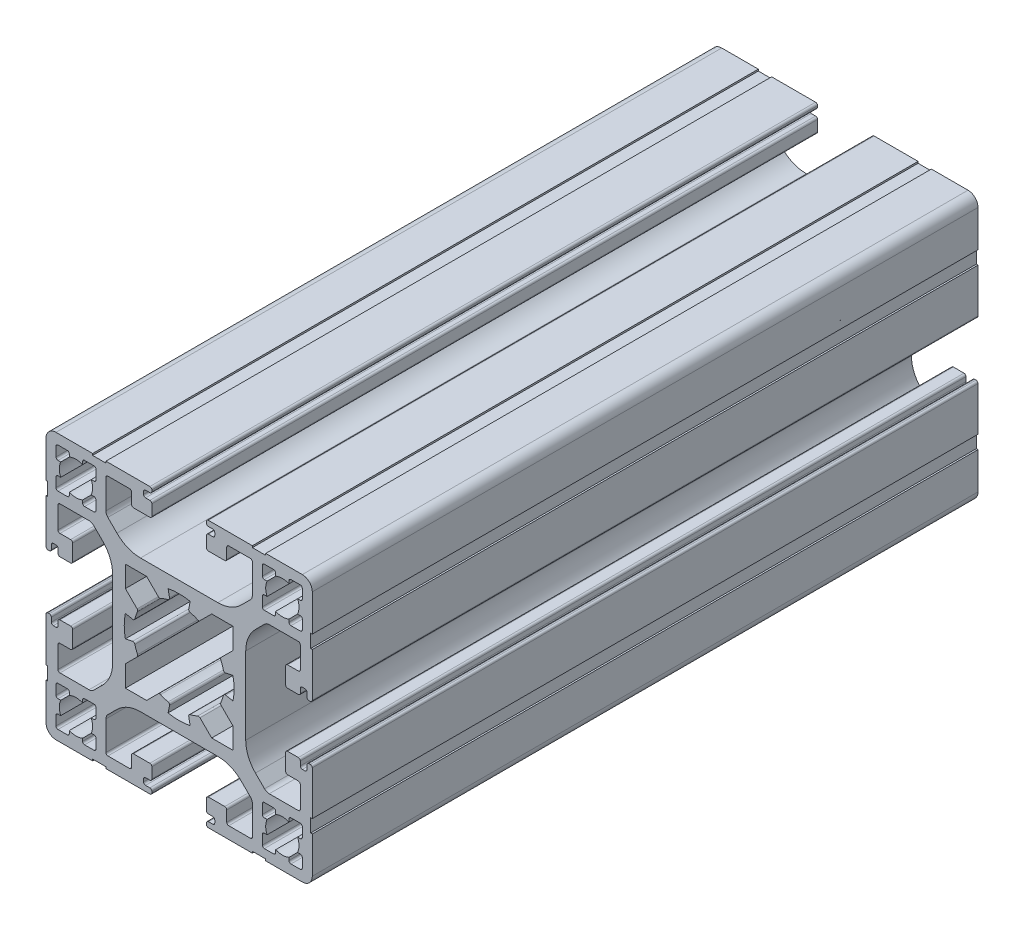
SolidWorks part; units mm, degrees
ref_plane "Plano frontal" through (0, 0, 0) normal (0, 0, 1) x (1, 0, 0)
ref_plane "Plano superior" through (0, 0, 0) normal (0, 1, 0) x (1, 0, 0)
ref_plane "Plano direito" through (0, 0, 0) normal (1, 0, 0) x (0, 0, -1)
sketch "Esboço1" plane through (0, 0, 0) normal (1, 0, 0) x (0, 0, -1)
  line L0 (-50, 0) -> (50, 0)
  point P4 (0, 0)
  dimension "D1" = 100
other "Quadrado PF40-01 - PERFIL 4040 BÁSICO(1)"
ref_plane "Plano1" through (0, 0, 50) normal (0, 0, -1) x (0, -1, 0)
sketch "Sketch1" plane through (0, 0, 50) normal (0, 0, -1) x (0, -1, 0)
  line L0 (18.2, -16.5) -> (17.7913, -16.5)
  line L1 (18.5, -18.2) -> (18.5, -16.8)
  line L2 (16.8, -18.5) -> (18.2, -18.5)
  line L3 (16.5, -17.7913) -> (16.5, -18.2)
  line L4 (14.5, -18.2) -> (14.5, -17.7913)
  line L5 (12.8, -18.5) -> (14.2, -18.5)
  line L6 (12.5, -16.8) -> (12.5, -18.2)
  line L7 (13.2087, -16.5) -> (12.8, -16.5)
  line L8 (12.8, -14.5) -> (13.2087, -14.5)
  line L9 (12.5, -12.8) -> (12.5, -14.2)
  line L10 (14.2, -12.5) -> (12.8, -12.5)
  line L11 (14.5, -13.2087) -> (14.5, -12.8)
  line L12 (16.5, -12.8) -> (16.5, -13.2087)
  line L13 (18.2, -12.5) -> (16.8, -12.5)
  line L14 (18.5, -14.2) -> (18.5, -12.8)
  line L15 (17.7913, -14.5) -> (18.2, -14.5)
  line L16 (-6.9972, 1.4391) -> (-8.0809, 1.662)
  line L17 (-8.0711, 4.8891) -> (-6.3143, 3.1324)
  line L18 (-8.0711, 8.0711) -> (-8.0711, 4.8891)
  line L19 (-4.8891, 8.0711) -> (-8.0711, 8.0711)
  line L20 (-3.1324, 6.3143) -> (-4.8891, 8.0711)
  line L21 (-1.662, 8.0809) -> (-1.4391, 6.9972)
  line L22 (1.4391, 6.9972) -> (1.662, 8.0809)
  line L23 (4.8891, 8.0711) -> (3.1324, 6.3143)
  line L24 (8.0711, 8.0711) -> (4.8891, 8.0711)
  line L25 (8.0711, 4.8891) -> (8.0711, 8.0711)
  line L26 (6.3143, 3.1324) -> (8.0711, 4.8891)
  line L27 (8.0809, 1.662) -> (6.9972, 1.4391)
  line L28 (6.9972, -1.4391) -> (8.0809, -1.662)
  line L29 (8.0711, -4.8891) -> (6.3143, -3.1324)
  line L30 (8.0711, -8.0711) -> (8.0711, -4.8891)
  line L31 (4.8891, -8.0711) -> (8.0711, -8.0711)
  line L32 (3.1324, -6.3143) -> (4.8891, -8.0711)
  line L33 (1.662, -8.0809) -> (1.4391, -6.9972)
  line L34 (-1.4391, -6.9972) -> (-1.662, -8.0809)
  line L35 (-4.8891, -8.0711) -> (-3.1324, -6.3143)
  line L36 (-8.0711, -8.0711) -> (-4.8891, -8.0711)
  line L37 (-8.0711, -4.8891) -> (-8.0711, -8.0711)
  line L38 (-6.3143, -3.1324) -> (-8.0711, -4.8891)
  line L39 (-8.0809, -1.662) -> (-6.9972, -1.4391)
  line L40 (-9.3431, 11.4645) -> (-10.7071, 12.8284)
  line L41 (-11, 13.5355) -> (-11, 17.9)
  line L42 (-10.7, 18.2) -> (-7.45, 18.2)
  line L43 (-7.15, 17.9) -> (-7.15, 16.3)
  line L44 (-6.85, 16) -> (-4.4, 16)
  line L45 (-4.1, 16.3) -> (-4.1, 17.9)
  line L46 (-4.4, 18.2) -> (-5.05, 18.2)
  line L47 (-5.35, 18.5) -> (-5.35, 18.9)
  line L48 (-5.05, 19.2) -> (-4.4, 19.2)
  line L49 (-4.1, 19.5) -> (-4.1, 19.7)
  line L50 (-4.4, 20) -> (-11, 20)
  line L51 (-11, 20) -> (-11, 19.75)
  line L52 (-11, 19.75) -> (-13, 19.75)
  line L53 (-13, 19.75) -> (-13, 20)
  line L54 (-13, 20) -> (-18.5, 20)
  line L55 (-20, 18.5) -> (-20, 13)
  line L56 (-20, 13) -> (-19.75, 13)
  line L57 (-19.75, 13) -> (-19.75, 11)
  line L58 (-19.75, 11) -> (-20, 11)
  line L59 (-20, 11) -> (-20, 4.4)
  line L60 (-19.7, 4.1) -> (-19.5, 4.1)
  line L61 (-19.2, 4.4) -> (-19.2, 5.05)
  line L62 (-18.9, 5.35) -> (-18.5, 5.35)
  line L63 (-18.2, 5.05) -> (-18.2, 4.4)
  line L64 (-17.9, 4.1) -> (-16.3, 4.1)
  line L65 (-16, 4.4) -> (-16, 6.85)
  line L66 (-16.3, 7.15) -> (-17.9, 7.15)
  line L67 (-18.2, 7.45) -> (-18.2, 10.7)
  line L68 (-17.9, 11) -> (-13.5355, 11)
  line L69 (-12.8284, 10.7071) -> (-11.4645, 9.3431)
  line L70 (-10, 5.8076) -> (-10, -5.8076)
  line L71 (-11.4645, -9.3431) -> (-12.8284, -10.7071)
  line L72 (-13.5355, -11) -> (-17.9, -11)
  line L73 (-18.2, -10.7) -> (-18.2, -7.45)
  line L74 (-17.9, -7.15) -> (-16.3, -7.15)
  line L75 (-16, -6.85) -> (-16, -4.4)
  line L76 (-16.3, -4.1) -> (-17.9, -4.1)
  line L77 (-18.2, -4.4) -> (-18.2, -5.05)
  line L78 (-18.5, -5.35) -> (-18.9, -5.35)
  line L79 (-19.2, -5.05) -> (-19.2, -4.4)
  line L80 (-19.5, -4.1) -> (-19.7, -4.1)
  line L81 (-20, -4.4) -> (-20, -11)
  line L82 (-20, -11) -> (-19.75, -11)
  line L83 (-19.75, -11) -> (-19.75, -13)
  line L84 (-19.75, -13) -> (-20, -13)
  line L85 (-20, -13) -> (-20, -18.5)
  line L86 (-18.5, -20) -> (-13, -20)
  line L87 (-13, -20) -> (-13, -19.75)
  line L88 (-13, -19.75) -> (-11, -19.75)
  line L89 (-11, -19.75) -> (-11, -20)
  line L90 (-11, -20) -> (-4.4, -20)
  line L91 (-4.1, -19.7) -> (-4.1, -19.5)
  line L92 (-4.4, -19.2) -> (-5.05, -19.2)
  line L93 (-5.35, -18.9) -> (-5.35, -18.5)
  line L94 (-5.05, -18.2) -> (-4.4, -18.2)
  line L95 (-4.1, -17.9) -> (-4.1, -16.3)
  line L96 (-4.4, -16) -> (-6.85, -16)
  line L97 (-7.15, -16.3) -> (-7.15, -17.9)
  line L98 (-7.45, -18.2) -> (-10.7, -18.2)
  line L99 (-11, -17.9) -> (-11, -13.5355)
  line L100 (-10.7071, -12.8284) -> (-9.3431, -11.4645)
  line L101 (-5.8076, -10) -> (5.8076, -10)
  line L102 (9.3431, -11.4645) -> (10.7071, -12.8284)
  line L103 (11, -13.5355) -> (11, -17.9)
  line L104 (10.7, -18.2) -> (7.45, -18.2)
  line L105 (7.15, -17.9) -> (7.15, -16.3)
  line L106 (6.85, -16) -> (4.4, -16)
  line L107 (4.1, -16.3) -> (4.1, -17.9)
  line L108 (4.4, -18.2) -> (5.05, -18.2)
  line L109 (5.35, -18.5) -> (5.35, -18.9)
  line L110 (5.05, -19.2) -> (4.4, -19.2)
  line L111 (4.1, -19.5) -> (4.1, -19.7)
  line L112 (4.4, -20) -> (11, -20)
  line L113 (11, -20) -> (11, -19.75)
  line L114 (11, -19.75) -> (13, -19.75)
  line L115 (13, -19.75) -> (13, -20)
  line L116 (13, -20) -> (18.5, -20)
  line L117 (20, -18.5) -> (20, -13)
  line L118 (20, -13) -> (19.75, -13)
  line L119 (19.75, -13) -> (19.75, -11)
  line L120 (19.75, -11) -> (20, -11)
  line L121 (20, -11) -> (20, -4.4)
  line L122 (19.7, -4.1) -> (19.5, -4.1)
  line L123 (19.2, -4.4) -> (19.2, -5.05)
  line L124 (18.9, -5.35) -> (18.5, -5.35)
  line L125 (18.2, -5.05) -> (18.2, -4.4)
  line L126 (17.9, -4.1) -> (16.3, -4.1)
  line L127 (16, -4.4) -> (16, -6.85)
  line L128 (16.3, -7.15) -> (17.9, -7.15)
  line L129 (18.2, -7.45) -> (18.2, -10.7)
  line L130 (17.9, -11) -> (13.5355, -11)
  line L131 (12.8284, -10.7071) -> (11.4645, -9.3431)
  line L132 (10, -5.8076) -> (10, 5.8076)
  line L133 (11.4645, 9.3431) -> (12.8284, 10.7071)
  line L134 (13.5355, 11) -> (17.9, 11)
  line L135 (18.2, 10.7) -> (18.2, 7.45)
  line L136 (17.9, 7.15) -> (16.3, 7.15)
  line L137 (16, 6.85) -> (16, 4.4)
  line L138 (16.3, 4.1) -> (17.9, 4.1)
  line L139 (18.2, 4.4) -> (18.2, 5.05)
  line L140 (18.5, 5.35) -> (18.9, 5.35)
  line L141 (19.2, 5.05) -> (19.2, 4.4)
  line L142 (19.5, 4.1) -> (19.7, 4.1)
  line L143 (20, 4.4) -> (20, 11)
  line L144 (20, 11) -> (19.75, 11)
  line L145 (19.75, 11) -> (19.75, 13)
  line L146 (19.75, 13) -> (20, 13)
  line L147 (20, 13) -> (20, 18.5)
  line L148 (18.5, 20) -> (13, 20)
  line L149 (13, 20) -> (13, 19.75)
  line L150 (13, 19.75) -> (11, 19.75)
  line L151 (11, 19.75) -> (11, 20)
  line L152 (11, 20) -> (4.4, 20)
  line L153 (4.1, 19.7) -> (4.1, 19.5)
  line L154 (4.4, 19.2) -> (5.05, 19.2)
  line L155 (5.35, 18.9) -> (5.35, 18.5)
  line L156 (5.05, 18.2) -> (4.4, 18.2)
  line L157 (4.1, 17.9) -> (4.1, 16.3)
  line L158 (4.4, 16) -> (6.85, 16)
  line L159 (7.15, 16.3) -> (7.15, 17.9)
  line L160 (7.45, 18.2) -> (10.7, 18.2)
  line L161 (11, 17.9) -> (11, 13.5355)
  line L162 (10.7071, 12.8284) -> (9.3431, 11.4645)
  line L163 (5.8076, 10) -> (-5.8076, 10)
  line L164 (-16.5, 17.7913) -> (-16.5, 18.2)
  line L165 (-14.5, 18.2) -> (-14.5, 17.7913)
  line L166 (-12.8, 18.5) -> (-14.2, 18.5)
  line L167 (-12.5, 16.8) -> (-12.5, 18.2)
  line L168 (-13.2087, 16.5) -> (-12.8, 16.5)
  line L169 (-12.8, 14.5) -> (-13.2087, 14.5)
  line L170 (-12.5, 12.8) -> (-12.5, 14.2)
  line L171 (-14.2, 12.5) -> (-12.8, 12.5)
  line L172 (-14.5, 13.2087) -> (-14.5, 12.8)
  line L173 (-16.5, 12.8) -> (-16.5, 13.2087)
  line L174 (-18.2, 12.5) -> (-16.8, 12.5)
  line L175 (-18.5, 14.2) -> (-18.5, 12.8)
  line L176 (-17.7913, 14.5) -> (-18.2, 14.5)
  line L177 (-18.2, 16.5) -> (-17.7913, 16.5)
  line L178 (-18.5, 18.2) -> (-18.5, 16.8)
  line L179 (-16.8, 18.5) -> (-18.2, 18.5)
  line L180 (14.5, 17.7913) -> (14.5, 18.2)
  line L181 (16.5, 18.2) -> (16.5, 17.7913)
  line L182 (18.2, 18.5) -> (16.8, 18.5)
  line L183 (18.5, 16.8) -> (18.5, 18.2)
  line L184 (17.7913, 16.5) -> (18.2, 16.5)
  line L185 (18.2, 14.5) -> (17.7913, 14.5)
  line L186 (18.5, 12.8) -> (18.5, 14.2)
  line L187 (16.8, 12.5) -> (18.2, 12.5)
  line L188 (16.5, 13.2087) -> (16.5, 12.8)
  line L189 (14.5, 12.8) -> (14.5, 13.2087)
  line L190 (12.8, 12.5) -> (14.2, 12.5)
  line L191 (12.5, 14.2) -> (12.5, 12.8)
  line L192 (13.2087, 14.5) -> (12.8, 14.5)
  line L193 (12.8, 16.5) -> (13.2087, 16.5)
  line L194 (12.5, 18.2) -> (12.5, 16.8)
  line L195 (14.2, 18.5) -> (12.8, 18.5)
  line L196 (-14.5, -17.7913) -> (-14.5, -18.2)
  line L197 (-16.5, -18.2) -> (-16.5, -17.7913)
  line L198 (-18.2, -18.5) -> (-16.8, -18.5)
  line L199 (-18.5, -16.8) -> (-18.5, -18.2)
  line L200 (-17.7913, -16.5) -> (-18.2, -16.5)
  line L201 (-18.2, -14.5) -> (-17.7913, -14.5)
  line L202 (-18.5, -12.8) -> (-18.5, -14.2)
  line L203 (-16.8, -12.5) -> (-18.2, -12.5)
  line L204 (-16.5, -13.2087) -> (-16.5, -12.8)
  line L205 (-14.5, -12.8) -> (-14.5, -13.2087)
  line L206 (-12.8, -12.5) -> (-14.2, -12.5)
  line L207 (-12.5, -14.2) -> (-12.5, -12.8)
  line L208 (-13.2087, -14.5) -> (-12.8, -14.5)
  line L209 (-12.8, -16.5) -> (-13.2087, -16.5)
  line L210 (-12.5, -18.2) -> (-12.5, -16.8)
  line L211 (-14.2, -18.5) -> (-12.8, -18.5)
  arc A0 (18.5, -16.8) -> (18.2, -16.5) centre (18.2, -16.8) ccw
  arc A1 (18.2, -18.5) -> (18.5, -18.2) centre (18.2, -18.2) ccw
  arc A2 (16.5, -18.2) -> (16.8, -18.5) centre (16.8, -18.2) ccw
  arc A3 (14.5, -17.7913) -> (16.5, -17.7913) centre (15.5, -15.5) ccw
  arc A4 (14.2, -18.5) -> (14.5, -18.2) centre (14.2, -18.2) ccw
  arc A5 (12.5, -18.2) -> (12.8, -18.5) centre (12.8, -18.2) ccw
  arc A6 (12.8, -16.5) -> (12.5, -16.8) centre (12.8, -16.8) ccw
  arc A7 (13.2087, -14.5) -> (13.2087, -16.5) centre (15.5, -15.5) ccw
  arc A8 (12.5, -14.2) -> (12.8, -14.5) centre (12.8, -14.2) ccw
  arc A9 (12.8, -12.5) -> (12.5, -12.8) centre (12.8, -12.8) ccw
  arc A10 (14.5, -12.8) -> (14.2, -12.5) centre (14.2, -12.8) ccw
  arc A11 (16.5, -13.2087) -> (14.5, -13.2087) centre (15.5, -15.5) ccw
  arc A12 (16.8, -12.5) -> (16.5, -12.8) centre (16.8, -12.8) ccw
  arc A13 (18.5, -12.8) -> (18.2, -12.5) centre (18.2, -12.8) ccw
  arc A14 (18.2, -14.5) -> (18.5, -14.2) centre (18.2, -14.2) ccw
  arc A15 (17.7913, -16.5) -> (17.7913, -14.5) centre (15.5, -15.5) ccw
  arc A16 (-6.9972, 1.4391) -> (-6.6458, 1.6602) centre (-6.9368, 1.7329) ccw
  arc A17 (-6.2526, 2.7977) -> (-6.6458, 1.6602) centre (0, 0) ccw
  arc A18 (-6.2526, 2.7977) -> (-6.3143, 3.1324) centre (-6.5265, 2.9202) ccw
  arc A19 (-3.1324, 6.3143) -> (-2.7977, 6.2526) centre (-2.9202, 6.5265) ccw
  arc A20 (-1.6602, 6.6458) -> (-2.7977, 6.2526) centre (0, 0) ccw
  arc A21 (-1.6602, 6.6458) -> (-1.4391, 6.9972) centre (-1.7329, 6.9368) ccw
  arc A22 (1.662, 8.0809) -> (-1.662, 8.0809) centre (0, 0) ccw
  arc A23 (1.4391, 6.9972) -> (1.6602, 6.6458) centre (1.7329, 6.9368) ccw
  arc A24 (2.7977, 6.2526) -> (1.6602, 6.6458) centre (0, 0) ccw
  arc A25 (2.7977, 6.2526) -> (3.1324, 6.3143) centre (2.9202, 6.5265) ccw
  arc A26 (6.3143, 3.1324) -> (6.2526, 2.7977) centre (6.5265, 2.9202) ccw
  arc A27 (6.6458, 1.6602) -> (6.2526, 2.7977) centre (0, 0) ccw
  arc A28 (6.6458, 1.6602) -> (6.9972, 1.4391) centre (6.9368, 1.7329) ccw
  arc A29 (8.0809, -1.662) -> (8.0809, 1.662) centre (0, 0) ccw
  arc A30 (6.9972, -1.4391) -> (6.6458, -1.6602) centre (6.9368, -1.7329) ccw
  arc A31 (6.2526, -2.7977) -> (6.6458, -1.6602) centre (0, 0) ccw
  arc A32 (6.2526, -2.7977) -> (6.3143, -3.1324) centre (6.5265, -2.9202) ccw
  arc A33 (3.1324, -6.3143) -> (2.7977, -6.2526) centre (2.9202, -6.5265) ccw
  arc A34 (1.6602, -6.6458) -> (2.7977, -6.2526) centre (0, 0) ccw
  arc A35 (1.6602, -6.6458) -> (1.4391, -6.9972) centre (1.7329, -6.9368) ccw
  arc A36 (-1.662, -8.0809) -> (1.662, -8.0809) centre (0, 0) ccw
  arc A37 (-1.4391, -6.9972) -> (-1.6602, -6.6458) centre (-1.7329, -6.9368) ccw
  arc A38 (-2.7977, -6.2526) -> (-1.6602, -6.6458) centre (0, 0) ccw
  arc A39 (-2.7977, -6.2526) -> (-3.1324, -6.3143) centre (-2.9202, -6.5265) ccw
  arc A40 (-6.3143, -3.1324) -> (-6.2526, -2.7977) centre (-6.5265, -2.9202) ccw
  arc A41 (-6.6458, -1.6602) -> (-6.2526, -2.7977) centre (0, 0) ccw
  arc A42 (-6.6458, -1.6602) -> (-6.9972, -1.4391) centre (-6.9368, -1.7329) ccw
  arc A43 (-8.0809, 1.662) -> (-8.0809, -1.662) centre (0, 0) ccw
  arc A44 (-9.3431, 11.4645) -> (-5.8076, 10) centre (-5.8076, 15) ccw
  arc A45 (-11, 13.5355) -> (-10.7071, 12.8284) centre (-10, 13.5355) ccw
  arc A46 (-10.7, 18.2) -> (-11, 17.9) centre (-10.7, 17.9) ccw
  arc A47 (-7.15, 17.9) -> (-7.45, 18.2) centre (-7.45, 17.9) ccw
  arc A48 (-7.15, 16.3) -> (-6.85, 16) centre (-6.85, 16.3) ccw
  arc A49 (-4.4, 16) -> (-4.1, 16.3) centre (-4.4, 16.3) ccw
  arc A50 (-4.1, 17.9) -> (-4.4, 18.2) centre (-4.4, 17.9) ccw
  arc A51 (-5.35, 18.5) -> (-5.05, 18.2) centre (-5.05, 18.5) ccw
  arc A52 (-5.05, 19.2) -> (-5.35, 18.9) centre (-5.05, 18.9) ccw
  arc A53 (-4.4, 19.2) -> (-4.1, 19.5) centre (-4.4, 19.5) ccw
  arc A54 (-4.1, 19.7) -> (-4.4, 20) centre (-4.4, 19.7) ccw
  arc A55 (-18.5, 20) -> (-20, 18.5) centre (-18.5, 18.5) ccw
  arc A56 (-20, 4.4) -> (-19.7, 4.1) centre (-19.7, 4.4) ccw
  arc A57 (-19.5, 4.1) -> (-19.2, 4.4) centre (-19.5, 4.4) ccw
  arc A58 (-18.9, 5.35) -> (-19.2, 5.05) centre (-18.9, 5.05) ccw
  arc A59 (-18.2, 5.05) -> (-18.5, 5.35) centre (-18.5, 5.05) ccw
  arc A60 (-18.2, 4.4) -> (-17.9, 4.1) centre (-17.9, 4.4) ccw
  arc A61 (-16.3, 4.1) -> (-16, 4.4) centre (-16.3, 4.4) ccw
  arc A62 (-16, 6.85) -> (-16.3, 7.15) centre (-16.3, 6.85) ccw
  arc A63 (-18.2, 7.45) -> (-17.9, 7.15) centre (-17.9, 7.45) ccw
  arc A64 (-17.9, 11) -> (-18.2, 10.7) centre (-17.9, 10.7) ccw
  arc A65 (-12.8284, 10.7071) -> (-13.5355, 11) centre (-13.5355, 10) ccw
  arc A66 (-10, 5.8076) -> (-11.4645, 9.3431) centre (-15, 5.8076) ccw
  arc A67 (-11.4645, -9.3431) -> (-10, -5.8076) centre (-15, -5.8076) ccw
  arc A68 (-13.5355, -11) -> (-12.8284, -10.7071) centre (-13.5355, -10) ccw
  arc A69 (-18.2, -10.7) -> (-17.9, -11) centre (-17.9, -10.7) ccw
  arc A70 (-17.9, -7.15) -> (-18.2, -7.45) centre (-17.9, -7.45) ccw
  arc A71 (-16.3, -7.15) -> (-16, -6.85) centre (-16.3, -6.85) ccw
  arc A72 (-16, -4.4) -> (-16.3, -4.1) centre (-16.3, -4.4) ccw
  arc A73 (-17.9, -4.1) -> (-18.2, -4.4) centre (-17.9, -4.4) ccw
  arc A74 (-18.5, -5.35) -> (-18.2, -5.05) centre (-18.5, -5.05) ccw
  arc A75 (-19.2, -5.05) -> (-18.9, -5.35) centre (-18.9, -5.05) ccw
  arc A76 (-19.2, -4.4) -> (-19.5, -4.1) centre (-19.5, -4.4) ccw
  arc A77 (-19.7, -4.1) -> (-20, -4.4) centre (-19.7, -4.4) ccw
  arc A78 (-20, -18.5) -> (-18.5, -20) centre (-18.5, -18.5) ccw
  arc A79 (-4.4, -20) -> (-4.1, -19.7) centre (-4.4, -19.7) ccw
  arc A80 (-4.1, -19.5) -> (-4.4, -19.2) centre (-4.4, -19.5) ccw
  arc A81 (-5.35, -18.9) -> (-5.05, -19.2) centre (-5.05, -18.9) ccw
  arc A82 (-5.05, -18.2) -> (-5.35, -18.5) centre (-5.05, -18.5) ccw
  arc A83 (-4.4, -18.2) -> (-4.1, -17.9) centre (-4.4, -17.9) ccw
  arc A84 (-4.1, -16.3) -> (-4.4, -16) centre (-4.4, -16.3) ccw
  arc A85 (-6.85, -16) -> (-7.15, -16.3) centre (-6.85, -16.3) ccw
  arc A86 (-7.45, -18.2) -> (-7.15, -17.9) centre (-7.45, -17.9) ccw
  arc A87 (-11, -17.9) -> (-10.7, -18.2) centre (-10.7, -17.9) ccw
  arc A88 (-10.7071, -12.8284) -> (-11, -13.5355) centre (-10, -13.5355) ccw
  arc A89 (-5.8076, -10) -> (-9.3431, -11.4645) centre (-5.8076, -15) ccw
  arc A90 (9.3431, -11.4645) -> (5.8076, -10) centre (5.8076, -15) ccw
  arc A91 (11, -13.5355) -> (10.7071, -12.8284) centre (10, -13.5355) ccw
  arc A92 (10.7, -18.2) -> (11, -17.9) centre (10.7, -17.9) ccw
  arc A93 (7.15, -17.9) -> (7.45, -18.2) centre (7.45, -17.9) ccw
  arc A94 (7.15, -16.3) -> (6.85, -16) centre (6.85, -16.3) ccw
  arc A95 (4.4, -16) -> (4.1, -16.3) centre (4.4, -16.3) ccw
  arc A96 (4.1, -17.9) -> (4.4, -18.2) centre (4.4, -17.9) ccw
  arc A97 (5.35, -18.5) -> (5.05, -18.2) centre (5.05, -18.5) ccw
  arc A98 (5.05, -19.2) -> (5.35, -18.9) centre (5.05, -18.9) ccw
  arc A99 (4.4, -19.2) -> (4.1, -19.5) centre (4.4, -19.5) ccw
  arc A100 (4.1, -19.7) -> (4.4, -20) centre (4.4, -19.7) ccw
  arc A101 (18.5, -20) -> (20, -18.5) centre (18.5, -18.5) ccw
  arc A102 (20, -4.4) -> (19.7, -4.1) centre (19.7, -4.4) ccw
  arc A103 (19.5, -4.1) -> (19.2, -4.4) centre (19.5, -4.4) ccw
  arc A104 (18.9, -5.35) -> (19.2, -5.05) centre (18.9, -5.05) ccw
  arc A105 (18.2, -5.05) -> (18.5, -5.35) centre (18.5, -5.05) ccw
  arc A106 (18.2, -4.4) -> (17.9, -4.1) centre (17.9, -4.4) ccw
  arc A107 (16.3, -4.1) -> (16, -4.4) centre (16.3, -4.4) ccw
  arc A108 (16, -6.85) -> (16.3, -7.15) centre (16.3, -6.85) ccw
  arc A109 (18.2, -7.45) -> (17.9, -7.15) centre (17.9, -7.45) ccw
  arc A110 (17.9, -11) -> (18.2, -10.7) centre (17.9, -10.7) ccw
  arc A111 (12.8284, -10.7071) -> (13.5355, -11) centre (13.5355, -10) ccw
  arc A112 (10, -5.8076) -> (11.4645, -9.3431) centre (15, -5.8076) ccw
  arc A113 (11.4645, 9.3431) -> (10, 5.8076) centre (15, 5.8076) ccw
  arc A114 (13.5355, 11) -> (12.8284, 10.7071) centre (13.5355, 10) ccw
  arc A115 (18.2, 10.7) -> (17.9, 11) centre (17.9, 10.7) ccw
  arc A116 (17.9, 7.15) -> (18.2, 7.45) centre (17.9, 7.45) ccw
  arc A117 (16.3, 7.15) -> (16, 6.85) centre (16.3, 6.85) ccw
  arc A118 (16, 4.4) -> (16.3, 4.1) centre (16.3, 4.4) ccw
  arc A119 (17.9, 4.1) -> (18.2, 4.4) centre (17.9, 4.4) ccw
  arc A120 (18.5, 5.35) -> (18.2, 5.05) centre (18.5, 5.05) ccw
  arc A121 (19.2, 5.05) -> (18.9, 5.35) centre (18.9, 5.05) ccw
  arc A122 (19.2, 4.4) -> (19.5, 4.1) centre (19.5, 4.4) ccw
  arc A123 (19.7, 4.1) -> (20, 4.4) centre (19.7, 4.4) ccw
  arc A124 (20, 18.5) -> (18.5, 20) centre (18.5, 18.5) ccw
  arc A125 (4.4, 20) -> (4.1, 19.7) centre (4.4, 19.7) ccw
  arc A126 (4.1, 19.5) -> (4.4, 19.2) centre (4.4, 19.5) ccw
  arc A127 (5.35, 18.9) -> (5.05, 19.2) centre (5.05, 18.9) ccw
  arc A128 (5.05, 18.2) -> (5.35, 18.5) centre (5.05, 18.5) ccw
  arc A129 (4.4, 18.2) -> (4.1, 17.9) centre (4.4, 17.9) ccw
  arc A130 (4.1, 16.3) -> (4.4, 16) centre (4.4, 16.3) ccw
  arc A131 (6.85, 16) -> (7.15, 16.3) centre (6.85, 16.3) ccw
  arc A132 (7.45, 18.2) -> (7.15, 17.9) centre (7.45, 17.9) ccw
  arc A133 (11, 17.9) -> (10.7, 18.2) centre (10.7, 17.9) ccw
  arc A134 (10.7071, 12.8284) -> (11, 13.5355) centre (10, 13.5355) ccw
  arc A135 (5.8076, 10) -> (9.3431, 11.4645) centre (5.8076, 15) ccw
  arc A136 (-14.5, 17.7913) -> (-16.5, 17.7913) centre (-15.5, 15.5) ccw
  arc A137 (-14.2, 18.5) -> (-14.5, 18.2) centre (-14.2, 18.2) ccw
  arc A138 (-12.5, 18.2) -> (-12.8, 18.5) centre (-12.8, 18.2) ccw
  arc A139 (-12.8, 16.5) -> (-12.5, 16.8) centre (-12.8, 16.8) ccw
  arc A140 (-13.2087, 14.5) -> (-13.2087, 16.5) centre (-15.5, 15.5) ccw
  arc A141 (-12.5, 14.2) -> (-12.8, 14.5) centre (-12.8, 14.2) ccw
  arc A142 (-12.8, 12.5) -> (-12.5, 12.8) centre (-12.8, 12.8) ccw
  arc A143 (-14.5, 12.8) -> (-14.2, 12.5) centre (-14.2, 12.8) ccw
  arc A144 (-16.5, 13.2087) -> (-14.5, 13.2087) centre (-15.5, 15.5) ccw
  arc A145 (-16.8, 12.5) -> (-16.5, 12.8) centre (-16.8, 12.8) ccw
  arc A146 (-18.5, 12.8) -> (-18.2, 12.5) centre (-18.2, 12.8) ccw
  arc A147 (-18.2, 14.5) -> (-18.5, 14.2) centre (-18.2, 14.2) ccw
  arc A148 (-17.7913, 16.5) -> (-17.7913, 14.5) centre (-15.5, 15.5) ccw
  arc A149 (-18.5, 16.8) -> (-18.2, 16.5) centre (-18.2, 16.8) ccw
  arc A150 (-18.2, 18.5) -> (-18.5, 18.2) centre (-18.2, 18.2) ccw
  arc A151 (-16.5, 18.2) -> (-16.8, 18.5) centre (-16.8, 18.2) ccw
  arc A152 (16.5, 17.7913) -> (14.5, 17.7913) centre (15.5, 15.5) ccw
  arc A153 (16.8, 18.5) -> (16.5, 18.2) centre (16.8, 18.2) ccw
  arc A154 (18.5, 18.2) -> (18.2, 18.5) centre (18.2, 18.2) ccw
  arc A155 (18.2, 16.5) -> (18.5, 16.8) centre (18.2, 16.8) ccw
  arc A156 (17.7913, 14.5) -> (17.7913, 16.5) centre (15.5, 15.5) ccw
  arc A157 (18.5, 14.2) -> (18.2, 14.5) centre (18.2, 14.2) ccw
  arc A158 (18.2, 12.5) -> (18.5, 12.8) centre (18.2, 12.8) ccw
  arc A159 (16.5, 12.8) -> (16.8, 12.5) centre (16.8, 12.8) ccw
  arc A160 (14.5, 13.2087) -> (16.5, 13.2087) centre (15.5, 15.5) ccw
  arc A161 (14.2, 12.5) -> (14.5, 12.8) centre (14.2, 12.8) ccw
  arc A162 (12.5, 12.8) -> (12.8, 12.5) centre (12.8, 12.8) ccw
  arc A163 (12.8, 14.5) -> (12.5, 14.2) centre (12.8, 14.2) ccw
  arc A164 (13.2087, 16.5) -> (13.2087, 14.5) centre (15.5, 15.5) ccw
  arc A165 (12.5, 16.8) -> (12.8, 16.5) centre (12.8, 16.8) ccw
  arc A166 (12.8, 18.5) -> (12.5, 18.2) centre (12.8, 18.2) ccw
  arc A167 (14.5, 18.2) -> (14.2, 18.5) centre (14.2, 18.2) ccw
  arc A168 (-16.5, -17.7913) -> (-14.5, -17.7913) centre (-15.5, -15.5) ccw
  arc A169 (-16.8, -18.5) -> (-16.5, -18.2) centre (-16.8, -18.2) ccw
  arc A170 (-18.5, -18.2) -> (-18.2, -18.5) centre (-18.2, -18.2) ccw
  arc A171 (-18.2, -16.5) -> (-18.5, -16.8) centre (-18.2, -16.8) ccw
  arc A172 (-17.7913, -14.5) -> (-17.7913, -16.5) centre (-15.5, -15.5) ccw
  arc A173 (-18.5, -14.2) -> (-18.2, -14.5) centre (-18.2, -14.2) ccw
  arc A174 (-18.2, -12.5) -> (-18.5, -12.8) centre (-18.2, -12.8) ccw
  arc A175 (-16.5, -12.8) -> (-16.8, -12.5) centre (-16.8, -12.8) ccw
  arc A176 (-14.5, -13.2087) -> (-16.5, -13.2087) centre (-15.5, -15.5) ccw
  arc A177 (-14.2, -12.5) -> (-14.5, -12.8) centre (-14.2, -12.8) ccw
  arc A178 (-12.5, -12.8) -> (-12.8, -12.5) centre (-12.8, -12.8) ccw
  arc A179 (-12.8, -14.5) -> (-12.5, -14.2) centre (-12.8, -14.2) ccw
  arc A180 (-13.2087, -16.5) -> (-13.2087, -14.5) centre (-15.5, -15.5) ccw
  arc A181 (-12.5, -16.8) -> (-12.8, -16.5) centre (-12.8, -16.8) ccw
  arc A182 (-12.8, -18.5) -> (-12.5, -18.2) centre (-12.8, -18.2) ccw
  arc A183 (-14.5, -18.2) -> (-14.2, -18.5) centre (-14.2, -18.2) ccw
  point P557 (0, 20)
  point P558 (-20, 20)
  point P559 (20, 20)
  point P560 (20, 0)
  point P561 (20, -20)
  point P562 (0, -20)
  point P563 (-20, -20)
  point P564 (-20, 0)
  point P565 (0, 0)
  point P566 (0, 0)
